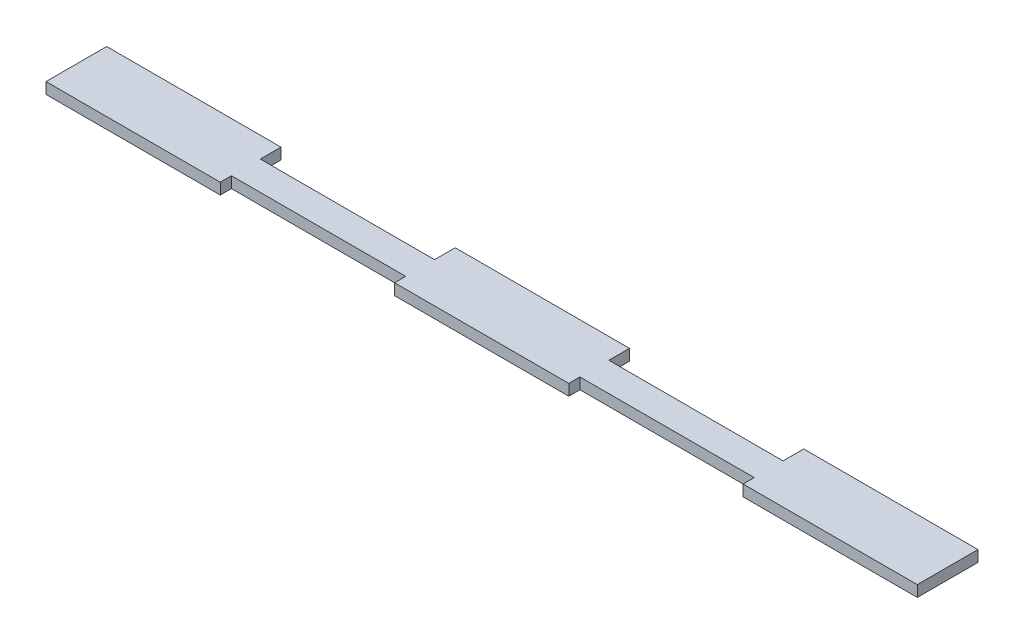
SolidWorks part; units mm, degrees
ref_plane "Front Plane" through (0, 0, 0) normal (0, 0, 1) x (1, 0, 0)
ref_plane "Top Plane" through (0, 0, 0) normal (0, 1, 0) x (1, 0, 0)
ref_plane "Right Plane" through (0, 0, 0) normal (1, 0, 0) x (0, 0, -1)
sketch "Sketch1" plane through (0, 0, 0) normal (0, 1, 0) x (1, 0, 0)
  line L0 (-63.3, 3.6876) -> (-21.1, 3.6876)
  line L1 (-105.5, 8.6876) -> (-63.3, 8.6876)
  line L2 (-105.5, 8.6876) -> (-105.5, -6.0124)
  line L3 (-105.5, -6.0124) -> (-63.3, -6.0124)
  line L4 (105.5, 8.6876) -> (105.5, -6.0124)
  line L5 (-63.3, -3.3124) -> (-21.1, -3.3124)
  line L7 (-21.1, 8.6876) -> (21.1, 8.6876)
  line L9 (63.3, 8.6876) -> (105.5, 8.6876)
  line L11 (-21.1, -6.0124) -> (21.1, -6.0124)
  line L13 (63.3, -6.0124) -> (105.5, -6.0124)
  line L14 (-63.3, 8.6876) -> (-63.3, 3.6876)
  line L15 (-63.3, -6.0124) -> (-63.3, -3.3124)
  line L16 (-21.1, 8.6876) -> (-21.1, 3.6876)
  line L17 (-21.1, -6.0124) -> (-21.1, -3.3124)
  line L18 (21.1, 8.6876) -> (21.1, 3.6876)
  line L19 (21.1, -6.0124) -> (21.1, -3.3124)
  line L20 (63.3, 8.6876) -> (63.3, 3.6876)
  line L21 (63.3, -6.0124) -> (63.3, -3.3124)
  line L22 (21.1, 3.6876) -> (63.3, 3.6876)
  line L23 (21.1, -3.3124) -> (63.3, -3.3124)
  point P0 (0, 0)
  dimension "D1" = 14.7
  dimension "D2" = 211
  dimension "D3" = 5
  dimension "D4" = 2.7
extrude "Boss-Extrude1" add sketch "Sketch1" along normal blind 2.7
